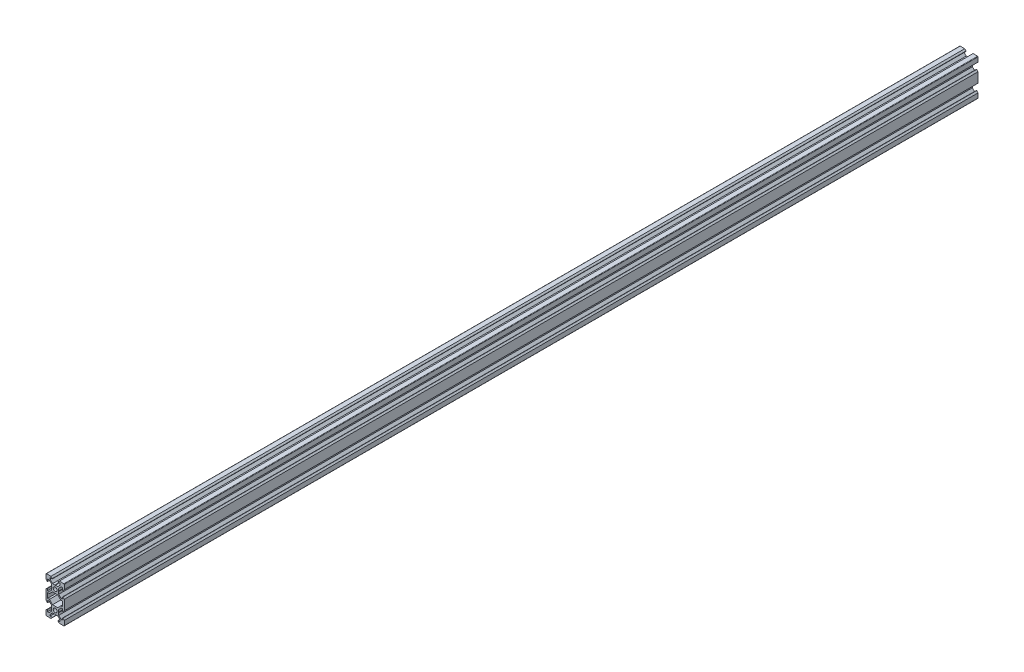
SolidWorks part; units mm, degrees
material "6061-T6 (SS)"
ref_plane "Front Plane" through (0, 0, 0) normal (0, 0, 1) x (1, 0, 0)
ref_plane "Top Plane" through (0, 0, 0) normal (0, 1, 0) x (1, 0, 0)
ref_plane "Right Plane" through (0, 0, 0) normal (1, 0, 0) x (0, 0, -1)
sketch "Sketch1" plane through (0, 0, 0) normal (0, 0, 1) x (1, 0, 0)
  line L0 (0, 0) -> (10, 0) construction
  line L1 (9.5, -20) -> (-9.5, -20)
  line L2 (10, -19.5) -> (10, 19.5)
  line L3 (9.5, 20) -> (-9.5, 20)
  line L4 (-10, -19.5) -> (-10, 19.5)
  line L5 (10, -20) -> (-10, 20) construction
  line L6 (10, 20) -> (-10, -20) construction
  circle A0 centre (0, 10) radius 2.1
  circle A1 centre (0, -10) radius 2.1
  arc A2 (-9.5, -20) -> (-10, -19.5) centre (-9.5, -19.5) cw
  arc A3 (9.5, -20) -> (10, -19.5) centre (9.5, -19.5) ccw
  arc A4 (10, 19.5) -> (9.5, 20) centre (9.5, 19.5) ccw
  arc A5 (-9.5, 20) -> (-10, 19.5) centre (-9.5, 19.5) ccw
  point P0 (0, 0)
  line B0 (0, 10) -> (0, 20) construction
  line B1 (0, 13.69) -> (-0.21, 13.9)
  line B2 (-0.21, 13.9) -> (-2.8393, 13.9)
  line B3 (-2.8393, 13.9) -> (-5.5, 16.5607)
  line B4 (-5.5, 16.5607) -> (-5.5, 18.2)
  line B5 (-5.5, 18.2) -> (-3.125, 18.2)
  line B6 (-3.125, 18.2) -> (-3.125, 18.545)
  line B7 (-3.125, 18.545) -> (-4.58, 20)
  line B8 (-4.58, 20) -> (4.58, 20)
  line B9 (0, 10) -> (-5.9132, 15.9132) construction
  line B10 (3.125, 18.545) -> (4.58, 20)
  line B11 (3.125, 18.2) -> (3.125, 18.545)
  line B12 (5.5, 18.2) -> (3.125, 18.2)
  line B13 (5.5, 16.5607) -> (5.5, 18.2)
  line B14 (2.8393, 13.9) -> (5.5, 16.5607)
  line B15 (0.21, 13.9) -> (2.8393, 13.9)
  line B16 (0, 13.69) -> (0.21, 13.9)
  line B17 (0, 10) -> (-10, 10) construction
  line B18 (-3.69, 10) -> (-3.9, 9.79)
  line B19 (-3.9, 9.79) -> (-3.9, 7.1607)
  line B20 (-3.9, 7.1607) -> (-6.5607, 4.5)
  line B21 (-6.5607, 4.5) -> (-8.2, 4.5)
  line B22 (-8.2, 4.5) -> (-8.2, 6.875)
  line B23 (-8.2, 6.875) -> (-8.545, 6.875)
  line B24 (-8.545, 6.875) -> (-10, 5.42)
  line B25 (-10, 5.42) -> (-10, 14.58)
  line B26 (0, 10) -> (-5.9132, 4.0868) construction
  line B27 (-8.545, 13.125) -> (-10, 14.58)
  line B28 (-8.2, 13.125) -> (-8.545, 13.125)
  line B29 (-8.2, 15.5) -> (-8.2, 13.125)
  line B30 (-6.5607, 15.5) -> (-8.2, 15.5)
  line B31 (-3.9, 12.8393) -> (-6.5607, 15.5)
  line B32 (-3.9, 10.21) -> (-3.9, 12.8393)
  line B33 (-3.69, 10) -> (-3.9, 10.21)
  line B34 (0, -10) -> (-10, -10) construction
  line B35 (-3.69, -10) -> (-3.9, -10.21)
  line B36 (-3.9, -10.21) -> (-3.9, -12.8393)
  line B37 (-3.9, -12.8393) -> (-6.5607, -15.5)
  line B38 (-6.5607, -15.5) -> (-8.2, -15.5)
  line B39 (-8.2, -15.5) -> (-8.2, -13.125)
  line B40 (-8.2, -13.125) -> (-8.545, -13.125)
  line B41 (-8.545, -13.125) -> (-10, -14.58)
  line B42 (-10, -14.58) -> (-10, -5.42)
  line B43 (0, -10) -> (-5.9132, -15.9132) construction
  line B44 (-8.545, -6.875) -> (-10, -5.42)
  line B45 (-8.2, -6.875) -> (-8.545, -6.875)
  line B46 (-8.2, -4.5) -> (-8.2, -6.875)
  line B47 (-6.5607, -4.5) -> (-8.2, -4.5)
  line B48 (-3.9, -7.1607) -> (-6.5607, -4.5)
  line B49 (-3.9, -9.79) -> (-3.9, -7.1607)
  line B50 (-3.69, -10) -> (-3.9, -9.79)
  line B51 (0, -10) -> (0, -20) construction
  line B52 (0, -13.69) -> (0.21, -13.9)
  line B53 (0.21, -13.9) -> (2.8393, -13.9)
  line B54 (2.8393, -13.9) -> (5.5, -16.5607)
  line B55 (5.5, -16.5607) -> (5.5, -18.2)
  line B56 (5.5, -18.2) -> (3.125, -18.2)
  line B57 (3.125, -18.2) -> (3.125, -18.545)
  line B58 (3.125, -18.545) -> (4.58, -20)
  line B59 (4.58, -20) -> (-4.58, -20)
  line B60 (0, -10) -> (5.9132, -15.9132) construction
  line B61 (-3.125, -18.545) -> (-4.58, -20)
  line B62 (-3.125, -18.2) -> (-3.125, -18.545)
  line B63 (-5.5, -18.2) -> (-3.125, -18.2)
  line B64 (-5.5, -16.5607) -> (-5.5, -18.2)
  line B65 (-2.8393, -13.9) -> (-5.5, -16.5607)
  line B66 (-0.21, -13.9) -> (-2.8393, -13.9)
  line B67 (0, -13.69) -> (-0.21, -13.9)
  line B68 (0, -10) -> (10, -10) construction
  line B69 (3.69, -10) -> (3.9, -9.79)
  line B70 (3.9, -9.79) -> (3.9, -7.1607)
  line B71 (3.9, -7.1607) -> (6.5607, -4.5)
  line B72 (6.5607, -4.5) -> (8.2, -4.5)
  line B73 (8.2, -4.5) -> (8.2, -6.875)
  line B74 (8.2, -6.875) -> (8.545, -6.875)
  line B75 (8.545, -6.875) -> (10, -5.42)
  line B76 (10, -5.42) -> (10, -14.58)
  line B77 (0, -10) -> (5.9132, -4.0868) construction
  line B78 (8.545, -13.125) -> (10, -14.58)
  line B79 (8.2, -13.125) -> (8.545, -13.125)
  line B80 (8.2, -15.5) -> (8.2, -13.125)
  line B81 (6.5607, -15.5) -> (8.2, -15.5)
  line B82 (3.9, -12.8393) -> (6.5607, -15.5)
  line B83 (3.9, -10.21) -> (3.9, -12.8393)
  line B84 (3.69, -10) -> (3.9, -10.21)
  line B85 (0, 10) -> (10, 10) construction
  line B86 (3.69, 10) -> (3.9, 10.21)
  line B87 (3.9, 10.21) -> (3.9, 12.8393)
  line B88 (3.9, 12.8393) -> (6.5607, 15.5)
  line B89 (6.5607, 15.5) -> (8.2, 15.5)
  line B90 (8.2, 15.5) -> (8.2, 13.125)
  line B91 (8.2, 13.125) -> (8.545, 13.125)
  line B92 (8.545, 13.125) -> (10, 14.58)
  line B93 (10, 14.58) -> (10, 5.42)
  line B94 (0, 10) -> (5.9132, 15.9132) construction
  line B95 (8.545, 6.875) -> (10, 5.42)
  line B96 (8.2, 6.875) -> (8.545, 6.875)
  line B97 (8.2, 4.5) -> (8.2, 6.875)
  line B98 (6.5607, 4.5) -> (8.2, 4.5)
  line B99 (3.9, 7.1607) -> (6.5607, 4.5)
  line B100 (3.9, 9.79) -> (3.9, 7.1607)
  line B101 (3.69, 10) -> (3.9, 9.79)
  line B102 (-8.2, -2.7) -> (-8.2, 2.7)
  line B103 (-8.2, 2.7) -> (-6.2393, 2.7)
  line B104 (-6.2393, 2.7) -> (-2.8393, 6.1)
  line B105 (-2.8393, 6.1) -> (2.8393, 6.1)
  line B106 (0, 6.1) -> (0, 0) construction
  line B107 (0, 0) -> (-8.2, 0) construction
  line B108 (6.2393, 2.7) -> (2.8393, 6.1)
  line B109 (8.2, 2.7) -> (6.2393, 2.7)
  line B110 (8.2, -2.7) -> (8.2, 2.7)
  line B111 (8.2, -2.7) -> (6.2393, -2.7)
  line B112 (6.2393, -2.7) -> (2.8393, -6.1)
  line B113 (-2.8393, -6.1) -> (2.8393, -6.1)
  line B114 (-6.2393, -2.7) -> (-2.8393, -6.1)
  line B115 (-8.2, -2.7) -> (-6.2393, -2.7)
  line B116 (0, 6.1) -> (0, 10) construction
  line B117 (0, 10) -> (-5.0927, 4.9073) construction
  dimension "D4" = 4.2
  dimension "D5" = 0.5
  dimension "D1" = 20
  dimension "D2" = 40
  dimension "D3" = 20
sketch_block_instance "V Slot 1-4"
sketch_block "V Slot 1" parameters "D1"=10, "D2"=11, "D3"=4.3, "D4"=1.8, "D5"=0.21, "D6"=45, "D7"=9.16, "D8"=1.5, "D9"=6.25
sketch_block_instance "V Slot 1-5"
sketch_block_instance "V Slot 1-6"
sketch_block_instance "V Slot 1-7"
sketch_block_instance "V Slot 1-8"
sketch_block_instance "V Slot 1-9"
sketch_block_instance "Center Cutout 1-1"
sketch_block "Center Cutout 1" parameters "D1"=5.4, "D2"=12.2, "D3"=8.2, "D4"=45, "D5"=10, "D6"=1.5
extrude "Boss-Extrude1" add sketch "Sketch1" along normal blind 1000 contours B101 B86 B87 B88 B89 B90 B91 B92 L2 A4 L3 B10 B11 B12 B13 B14 B15 B16 B1 B2 B3 B4 B5 B6 B7 A5 L4 B27 B28 B29 B30 B31 B32 B33 B18 B19 B20 B21 B22 B23 B24 B44 B45 B46 B47 B48 B49 B50 B35
